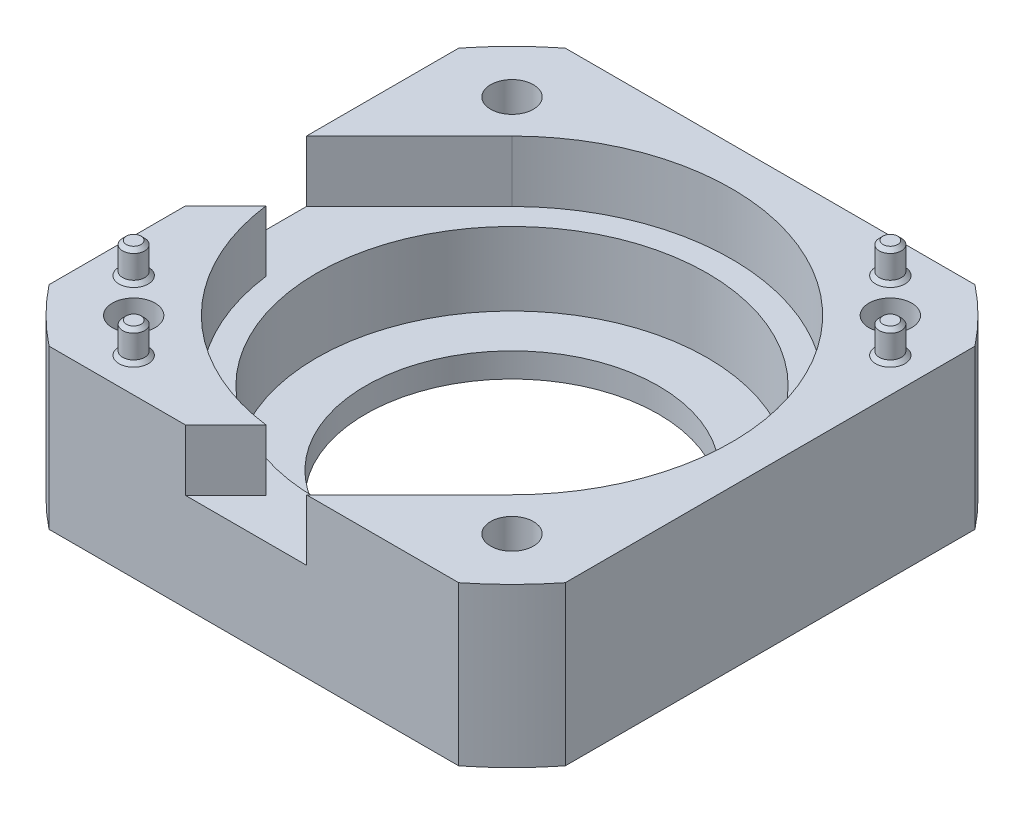
SolidWorks part; units mm, degrees
ref_plane "Front Plane" through (0, 0, 0) normal (0, 0, 1) x (1, 0, 0)
ref_plane "Top Plane" through (0, 0, 0) normal (0, 1, 0) x (1, 0, 0)
ref_plane "Right Plane" through (0, 0, 0) normal (1, 0, 0) x (0, 0, -1)
sketch "Sketch2" plane through (0, 0, 0) normal (0, 1, 0) x (1, 0, 0)
  line L1 (-21.15, 21.15) -> (21.15, 21.15)
  line L2 (-21.15, 21.15) -> (-21.15, -21.15)
  line L3 (-21.15, -21.15) -> (21.15, -21.15)
  line L4 (21.15, 21.15) -> (21.15, -21.15)
  line L5 (-21.15, 21.15) -> (21.15, -21.15) construction
  line L6 (-21.15, -21.15) -> (21.15, 21.15) construction
  point P0 (0, 0)
  dimension "D1" = 42.3
extrude "Boss-Extrude1" add sketch "Sketch2" along normal blind 13
sketch "Sketch3" plane through (0, 13, 0) normal (0, 1, 0) x (1, 0, 0)
  circle A0 centre (0, 0) radius 11
  dimension "D1" = 22
extrude "Cut-Extrude1" cut sketch "Sketch3" against normal through all
sketch "Sketch4" plane through (0, 13, 0) normal (0, 1, 0) x (1, 0, 0)
  line L1 (-15.5, 15.5) -> (15.5, 15.5) construction
  line L2 (-15.5, 15.5) -> (-15.5, -15.5) construction
  line L3 (-15.5, -15.5) -> (15.5, -15.5) construction
  line L4 (15.5, 15.5) -> (15.5, -15.5) construction
  line L5 (-15.5, 15.5) -> (15.5, -15.5) construction
  line L6 (-15.5, -15.5) -> (15.5, 15.5) construction
  circle A0 centre (-15.5, 15.5) radius 1.75
  circle A1 centre (15.5, 15.5) radius 1.75
  circle A2 centre (15.5, -15.5) radius 1.75
  circle A3 centre (-15.5, -15.5) radius 1.75
  point P0 (0, 0)
  point P16 (0, 0)
  dimension "D3" = 3.5
  dimension "D1" = 31
  dimension "D2" = 31
  dimension "D4" = 4
extrude "Cut-Extrude2" cut sketch "Sketch4" against normal through all
sketch "Sketch5" plane through (0, 13, 0) normal (0, 1, 0) x (1, 0, 0)
  circle A0 centre (0, 0) radius 27
  circle A1 centre (0, 0) radius 29.9106
  dimension "D1" = 54
extrude "Cut-Extrude4" cut sketch "Sketch5" against normal through all
sketch "Sketch6" plane through (0, 13, 0) normal (0, 1, 0) x (1, 0, 0)
  line L0 (-21.15, 4.3058) -> (-12.7279, 12.7279)
  line L1 (12.7279, -12.7279) -> (4.3058, -21.15)
  line L9 (-21.15, 16.7833) -> (-21.15, -16.7833) construction
  line L10 (-16.7833, -21.15) -> (16.7833, -21.15) construction
  line L11 (-7.7782, 7.7782) -> (-21.15, -5.5937) construction
  line L12 (4.3058, 21.15) -> (21.15, 4.3058) construction
  line L13 (7.3751, 21.15) -> (21.15, 7.3751) construction
  line L14 (16.7833, 21.15) -> (-16.7833, 21.15) construction
  line L15 (21.15, -16.7833) -> (21.15, 16.7833) construction
  line L18 (7.7782, -7.7782) -> (-5.5937, -21.15) construction
  line L19 (-21.15, 4.3058) -> (-21.15, -5.5937)
  line L21 (-2.2965, -17.8529) -> (-5.5937, -21.15)
  line L22 (-5.5937, -21.15) -> (4.3058, -21.15)
  line L23 (-17.8529, -2.2965) -> (-21.15, -5.5937)
  arc A0 (-12.7279, 12.7279) -> (12.7279, -12.7279) centre (0, 0) cw
  circle A2 centre (0, 0) radius 11 construction
  arc A4 (-12.7279, 12.7279) -> (12.7279, -12.7279) centre (0, 0) ccw construction
  circle A5 centre (15.5, 15.5) radius 1.75 construction
  arc A6 (-17.8529, -2.2965) -> (-2.2965, -17.8529) centre (0, 0) ccw
  dimension "D1" = 45
  dimension "D3" = 18
  dimension "D2" = 45
  dimension "D4" = 45
extrude "Cut-Extrude5" cut sketch "Sketch6" against normal offset from surface (11 mm away) 2 up to face at (-15.5, 0, 17.25)
sketch "Sketch7" plane through (0, 2, 0) normal (0, 1, 0) x (1, 0, 0)
  line L6 (-21.15, 4.3058) -> (-21.15, -5.5937)
  line L7 (-21.15, -5.5937) -> (-17.8529, -2.2965)
  line L8 (-2.2965, -17.8529) -> (-5.5937, -21.15)
  line L9 (-5.5937, -21.15) -> (4.3058, -21.15)
  line L10 (4.3058, -21.15) -> (12.7279, -12.7279)
  line L11 (-12.7279, 12.7279) -> (-21.15, 4.3058)
  line L12 (-21.15, 4.3058) -> (-21.15, -5.5937)
  line L13 (-21.15, -5.5937) -> (-17.8529, -2.2965)
  line L14 (-2.2965, -17.8529) -> (-5.5937, -21.15)
  line L15 (-5.5937, -21.15) -> (4.3058, -21.15)
  line L16 (4.3058, -21.15) -> (12.7279, -12.7279)
  line L17 (-12.7279, 12.7279) -> (-21.15, 4.3058)
  circle A0 centre (0, 0) radius 16
  arc A3 (-17.8529, -2.2965) -> (-2.2965, -17.8529) centre (0, 0) ccw
  arc A4 (12.7279, -12.7279) -> (-12.7279, 12.7279) centre (0, 0) ccw
  arc A5 (-17.8529, -2.2965) -> (-2.2965, -17.8529) centre (0, 0) ccw
  arc A6 (12.7279, -12.7279) -> (-12.7279, 12.7279) centre (0, 0) ccw
  dimension "D1" = 32
  dimension "D2" = 0
extrude "Boss-Extrude2" add sketch "Sketch7" along normal offset from surface (6 mm away) 5 up to face at (3.3942, 13, -3.3942)
sketch "Sketch8" plane through (0, 13, 0) normal (0, 1, 0) x (1, 0, 0)
  line L0 (12.6716, 18.3284) -> (18.3284, 12.6716) construction
  line L1 (4.3058, -21.15) -> (16.7833, -21.15) construction
  line L2 (-19.0919, 19.0919) -> (19.0919, -19.0919) construction
  line L3 (-18.3284, -12.6716) -> (-12.6716, -18.3284) construction
  circle A0 centre (15.5, 15.5) radius 1.75 construction
  circle A1 centre (12.6716, 18.3284) radius 0.9
  circle A2 centre (18.3284, 12.6716) radius 0.9
  arc A3 (-16.7833, 21.15) -> (-21.15, 16.7833) centre (0, 0) ccw construction
  arc A4 (16.7833, -21.15) -> (21.15, -16.7833) centre (0, 0) ccw construction
  circle A5 centre (-12.6716, -18.3284) radius 0.9
  circle A6 centre (-18.3284, -12.6716) radius 0.9
  point P2 (15.5, 15.5)
  dimension "D1" = 1.8
  dimension "D2" = 1.8
  dimension "D3" = 45
  dimension "D4" = 4
extrude "Boss-Extrude3" add sketch "Sketch8" along normal blind 2.5
chamfer "Chamfer1" distance 0.3 angle 45 4 edges at (18.3284, 15.5, -11.7716) (12.6716, 15.5, -17.4284) (-18.3284, 15.5, 11.7716) (-12.6716, 15.5, 17.4284)
chamfer "Chamfer2" distance 0.3 angle 45 4 edges at (18.3284, 13, -11.7716) (12.6716, 13, -17.4284) (-18.3284, 13, 11.7716) (-12.6716, 13, 17.4284)
sketch "Sketch9" plane through (0, 2, 0) normal (0, 1, 0) x (1, 0, 0)
  circle A0 centre (0, 0) radius 12
  dimension "D1" = 24
extrude "Cut-Extrude6" cut sketch "Sketch9" against normal through all
chamfer "Chamfer4" distance 0.5 angle 45 4 edges at (-15.5, 0, -13.75) (15.5, 0, -13.75) (-15.5, 0, 17.25) (15.5, 0, 17.25)
